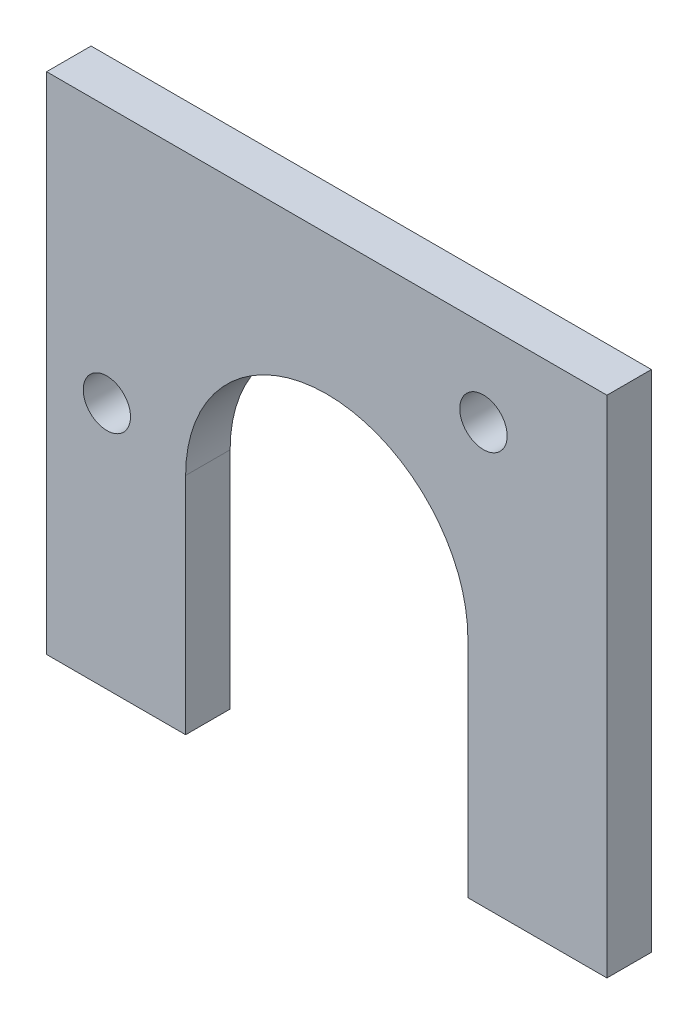
SolidWorks part; units mm, degrees
ref_plane "Front Plane" through (0, 0, 0) normal (0, 0, 1) x (1, 0, 0)
ref_plane "Top Plane" through (0, 0, 0) normal (0, 1, 0) x (1, 0, 0)
ref_plane "Right Plane" through (0, 0, 0) normal (1, 0, 0) x (0, 0, -1)
sketch "Sketch1" plane through (0, 0, 0) normal (0, 0, 1) x (1, 0, 0)
  line L0 (0, 0) -> (0, 5)
  line L1 (10.075, 5) -> (-10.075, 5)
  line L2 (-10.075, 5) -> (-10.075, -13.15)
  line L3 (-10.075, -13.15) -> (-5.075, -13.15)
  line L4 (-5.075, -13.15) -> (-5.075, -5.075)
  line L5 (5.075, -13.15) -> (5.075, -5.075)
  line L6 (10.075, -13.15) -> (5.075, -13.15)
  line L7 (10.075, 5) -> (10.075, -13.15)
  arc A0 (-5.075, -5.075) -> (5.075, -5.075) centre (0, -5.075) cw
  dimension "D1" = 5.075
  dimension "D2" = 13.15
  dimension "D3" = 5
  dimension "D4" = 5
extrude "Boss-Extrude1" add sketch "Sketch1" along normal blind 1.6 contours L1 L2 L3 L4 A0 L5 L6 L7
sketch "Sketch2" plane through (0, 0, 1.6) normal (0, 0, 1) x (1, 0, 0)
  circle A0 centre (5.6343, 1.9364) radius 0.8525
  circle A1 centre (-7.9078, -4.2424) radius 0.85
  dimension "D1" = 1.7
  dimension "D2" = 1.7049
extrude "Cut-Extrude1" cut sketch "Sketch2" against normal blind 3
